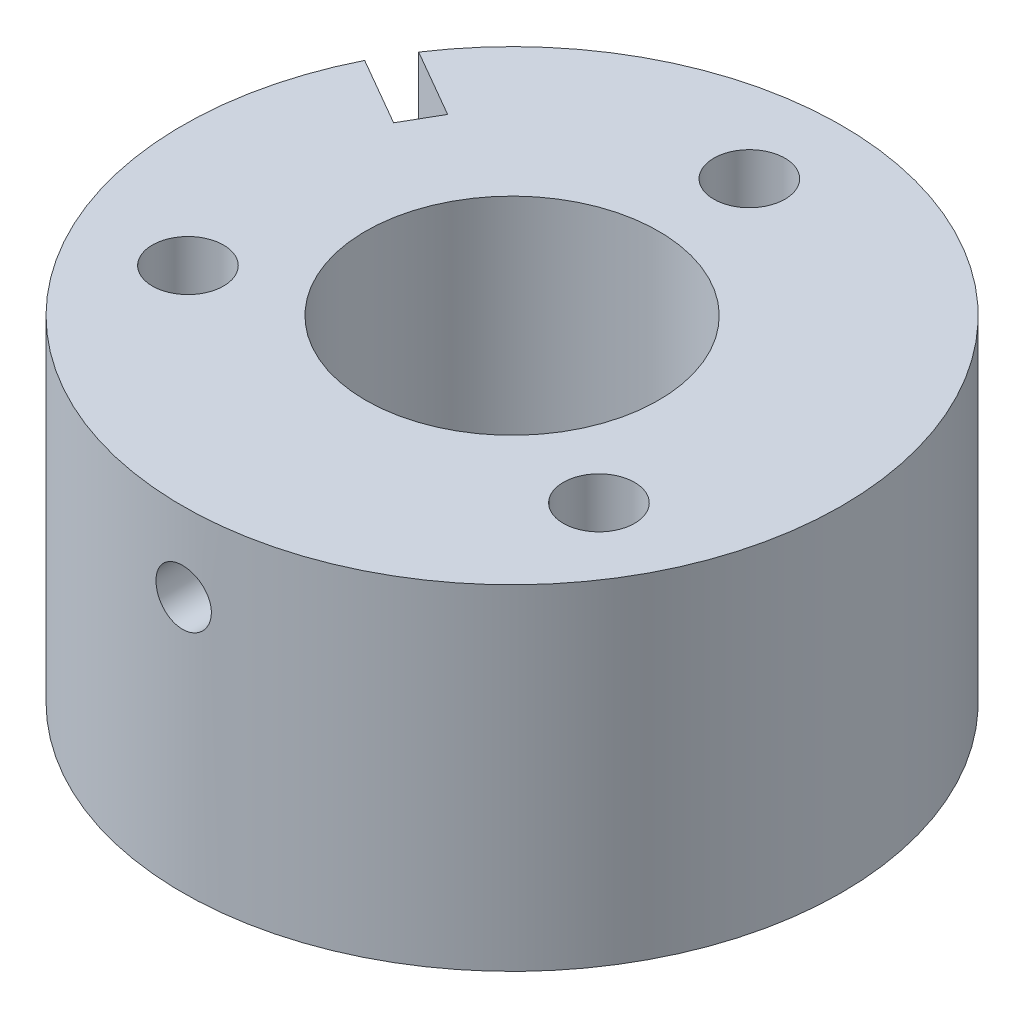
SolidWorks part; units mm, degrees
ref_plane "Front Plane" through (0, 0, 0) normal (0, 0, 1) x (1, 0, 0)
ref_plane "Top Plane" through (0, 0, 0) normal (0, 1, 0) x (1, 0, 0)
ref_plane "Right Plane" through (0, 0, 0) normal (1, 0, 0) x (0, 0, -1)
sketch "Sketch1" plane through (0, 0, 0) normal (0, 1, 0) x (1, 0, 0)
  line L0 (0, 0) -> (-29.1298, 16.8181) construction
  line L1 (-15.6655, 10.7765) -> (-20.8616, 13.7765)
  line L2 (-15.6655, 10.7765) -> (-17.1655, 8.1784)
  line L3 (0, 18) -> (-15.5885, -9) construction
  line L4 (-17.1655, 8.1784) -> (-22.3616, 11.1784)
  line L5 (-15.6655, 10.7765) -> (-22.3616, 11.1784) construction
  line L6 (-20.8616, 13.7765) -> (-17.1655, 8.1784) construction
  arc A0 (-22.3616, 11.1784) -> (-20.8616, 13.7765) centre (0, 0) ccw
  circle A1 centre (0, 0) radius 11.1125
  circle A2 centre (0, 18) radius 2.7
  circle A3 centre (15.5885, -9) radius 2.7
  circle A4 centre (-15.5885, -9) radius 2.7
  point P8 (-19.0136, 10.9775)
  point P13 (0, 0)
  dimension "D1" = 3
  dimension "D2" = 25
  dimension "D3" = 22.225
  dimension "D4" = 5.4
  dimension "D5" = 18
  dimension "D6" = 6
  dimension "D7" = 3
extrude "Boss-Extrude1" add sketch "Sketch1" along normal mid plane 25.4
hole_wizard "M5x0.8 Tapped Hole1" positions "3DSketch1" profile "Sketch2" tap size "M5x0.8" standard "ANSI Metric"
sketch3d "3DSketch1"
  point P0 (0, 6.7, 25)
  dimension "D1" = 6
sketch "Sketch2" plane through (0, 6.7, 25) normal (1, 0, 0) x (0, -1, 0)
  line L0 (0, 0) -> (0, 13.8875)
  line L1 (0, 13.8875) -> (2.1, 13.8875)
  line L2 (2.1, 13.8875) -> (2.1, 0)
  line L5 (2.1, 0) -> (0, 0)
  line L11 (0, -6.35) -> (0, 107.95) construction
  dimension "Thru Tap Drill Dia." = 4.2
  dimension "Thru Tap Drill Depth" = 13.8875
cosmetic thread "Hole Thread1" parameters "D2"=5
